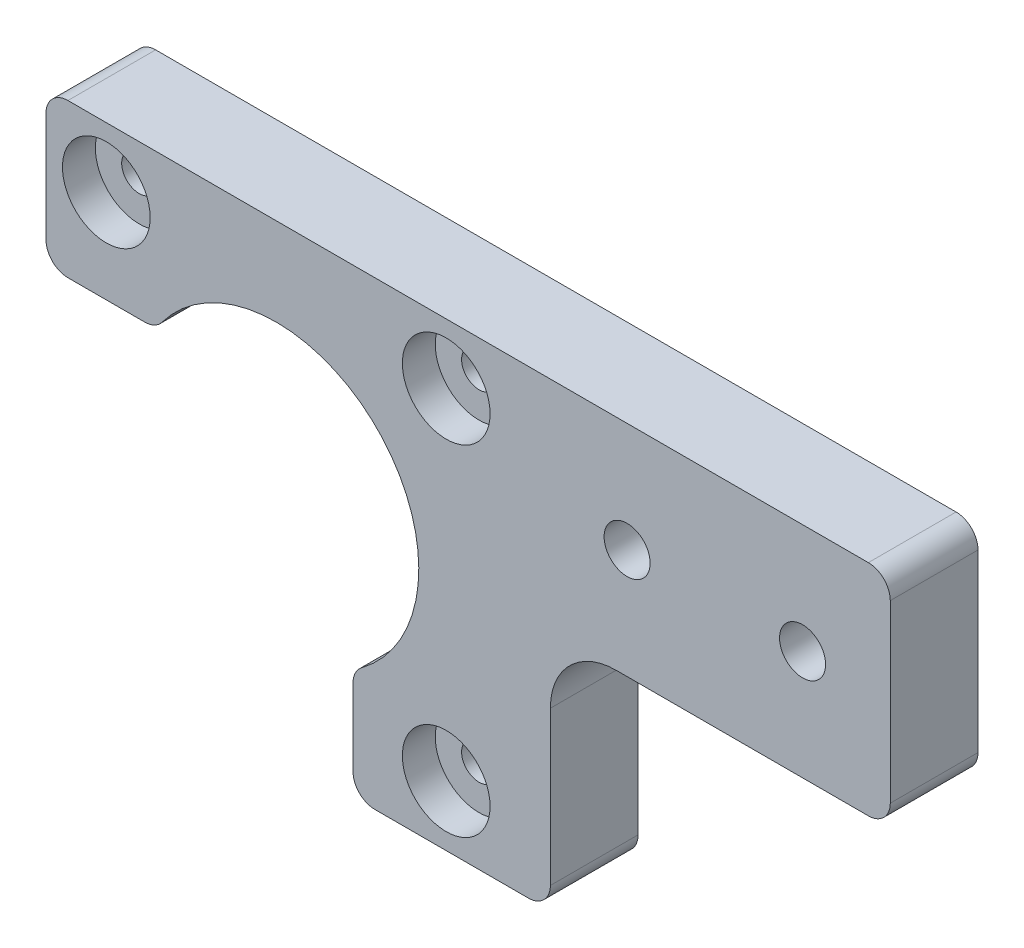
SolidWorks part; units mm, degrees
ref_plane "Plan de face" through (0, 0, 0) normal (0, 0, 1) x (1, 0, 0)
ref_plane "Plan de dessus" through (0, 0, 0) normal (0, 1, 0) x (1, 0, 0)
ref_plane "Plan de droite" through (0, 0, 0) normal (1, 0, 0) x (0, 0, -1)
sketch "Esquisse1" plane through (0, 0, 0) normal (0, 0, 1) x (1, 0, 0)
  line L1 (0, 0) -> (77, 0)
  line L2 (0, 0) -> (0, 42)
  line L3 (0, 42) -> (77, 42)
  line L4 (77, 0) -> (77, 42)
  dimension "D1" = 42
  dimension "D2" = 77
extrude "Boss.-Extru.1" add sketch "Esquisse1" along normal blind 8
sketch "Esquisse3" plane through (0, 0, 8) normal (0, 0, 1) x (1, 0, 0)
  line L0 (42, 42) -> (42, 0) construction
  line L1 (77, 42) -> (0, 42) construction
  line L2 (0, 0) -> (77, 0) construction
  line L3 (0, 42) -> (0, 0) construction
  circle A0 centre (5.5, 36.5) radius 4
  circle A1 centre (36.5, 36.5) radius 4
  circle A2 centre (36.5, 5.5) radius 4
  point P16 (42000, 7194.7051)
  point P17 (42000, 903.4088)
  dimension "D2" = 8
  dimension "D3" = 8
  dimension "D4" = 8
  dimension "D1" = 42
  dimension "D5" = 5.5
  dimension "D6" = 5.5
  dimension "D7" = 5.5
  dimension "D8" = 5.5
  dimension "D9" = 5.5
  dimension "D10" = 5.5
extrude "Enlèv. mat.-Extru.1" cut sketch "Esquisse3" against normal blind 3
sketch "Esquisse4" plane through (0, 0, 8) normal (0, 0, 1) x (1, 0, 0)
  line L0 (0, 42) -> (0, 0) construction
  line L1 (77, 42) -> (0, 42) construction
  circle A0 centre (21, 21) radius 13
  dimension "D1" = 26
  dimension "D2" = 21
  dimension "D3" = 21
extrude "Enlèv. mat.-Extru.2" cut sketch "Esquisse4" against normal through all
sketch "Esquisse5" plane through (0, 0, 8) normal (0, 0, 1) x (1, 0, 0)
  line L1 (0, 0) -> (28, 0)
  line L2 (0, 0) -> (0, 28)
  line L3 (0, 28) -> (28, 28)
  line L4 (28, 0) -> (28, 28)
  dimension "D1" = 28
  dimension "D2" = 28
extrude "Enlèv. mat.-Extru.3" cut sketch "Esquisse5" against normal through all
sketch "Esquisse10" plane through (0, 0, 5) normal (0, 0, 1) x (1, 0, 0)
  circle A0 centre (5.5, 36.5) radius 1.6
  circle A1 centre (36.5, 36.5) radius 1.6
  circle A2 centre (36.5, 5.5) radius 1.6
  dimension "D1" = 3.2
  dimension "D2" = 3.2
  dimension "D3" = 3.2
extrude "Enlèv. mat.-Extru.4" cut sketch "Esquisse10" against normal through all
sketch "Esquisse11" plane through (0, 0, 8) normal (0, 0, 1) x (1, 0, 0)
  line L0 (28, 0) -> (28, 10.0455) construction
  line L1 (77, 0) -> (46, 0)
  line L2 (77, 0) -> (77, 22)
  line L3 (77, 22) -> (46, 22)
  line L4 (46, 0) -> (46, 22)
  line L5 (77, 42) -> (0, 42) construction
  dimension "D1" = 18
  dimension "D2" = 20
extrude "Enlèv. mat.-Extru.5" cut sketch "Esquisse11" against normal through all
sketch "Esquisse12" plane through (0, 0, 8) normal (0, 0, 1) x (1, 0, 0)
  line L0 (77, 42) -> (0, 42) construction
  line L1 (77, 22) -> (77, 42) construction
  circle A0 centre (53, 32) radius 2.1
  circle A1 centre (69, 32) radius 2.1
  dimension "D1" = 4.2
  dimension "D2" = 4.2
  dimension "D3" = 10
  dimension "D4" = 10
  dimension "D5" = 8
  dimension "D6" = 16
extrude "Enlèv. mat.-Extru.6" cut sketch "Esquisse12" against normal through all
fillet "Congé1" radius 6 1 edges at (46, 22, 4)
fillet "Congé2" radius 2 8 edges at (28, 10.0455, 4) (0, 42, 4) (77, 42, 4) (77, 22, 4) (10.0455, 28, 4) (0, 28, 4) (28, 0, 4) (46, 0, 4)
